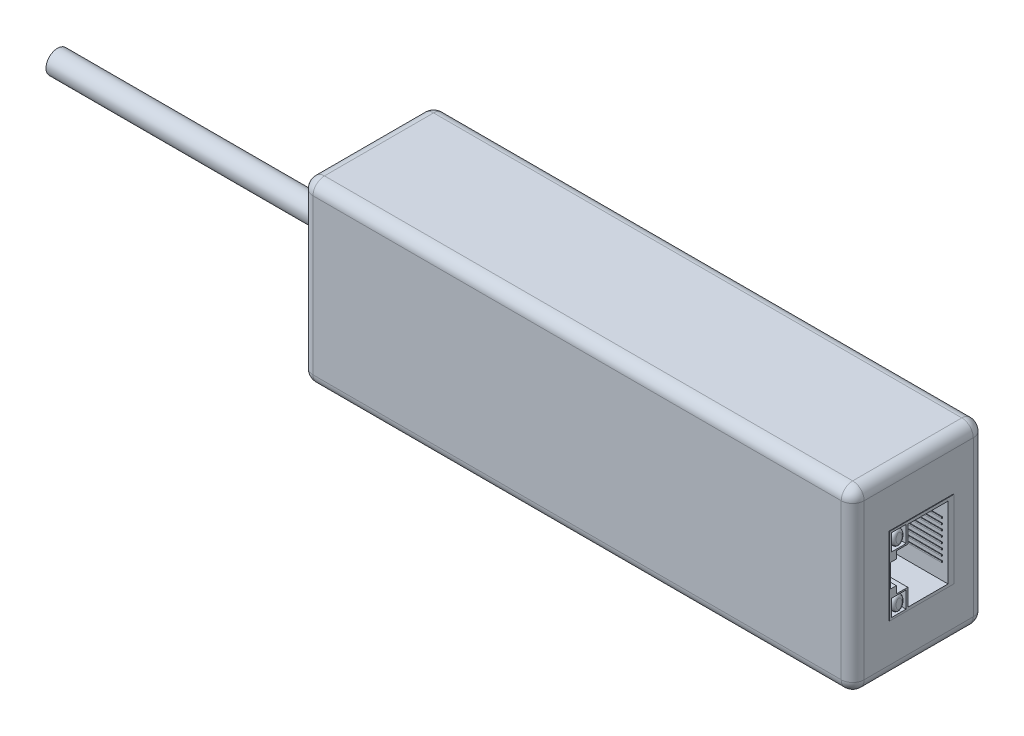
SolidWorks part; units mm, degrees
material "ABS"
ref_plane "前基準面" through (0, 0, 0) normal (0, 0, 1) x (1, 0, 0)
ref_plane "上基準面" through (0, 0, 0) normal (0, 1, 0) x (1, 0, 0)
ref_plane "右基準面" through (0, 0, 0) normal (1, 0, 0) x (0, 0, -1)
sketch "草圖1" plane through (0, 0, 0) normal (0, 0, 1) x (1, 0, 0)
  line L1 (-48, 15.5) -> (48, 15.5)
  line L2 (-48, 15.5) -> (-48, -15.5)
  line L3 (-48, -15.5) -> (48, -15.5)
  line L4 (48, 15.5) -> (48, -15.5)
  line L5 (-48, 15.5) -> (48, -15.5) construction
  line L6 (-48, -15.5) -> (48, 15.5) construction
  point P0 (0, 0)
  dimension "D1" = 96
  dimension "D2" = 31
extrude "填料-伸長1" add sketch "草圖1" along normal mid plane 23
sketch "草圖2" plane through (0, 0, -11.5) normal (0, 0, -1) x (-1, 0, 0)
  line L0 (20.25, 0) -> (3.25, 0) construction
  line L1 (23, -7) -> (17.5, -7)
  line L2 (23, -7) -> (23, 7)
  line L3 (23, 7) -> (17.5, 7)
  line L4 (17.5, -7) -> (17.5, 7)
  line L5 (23, -7) -> (17.5, 7) construction
  line L6 (23, 7) -> (17.5, -7) construction
  line L7 (6, -7) -> (0.5, -7)
  line L8 (6, -7) -> (6, 7)
  line L9 (6, 7) -> (0.5, 7)
  line L10 (0.5, -7) -> (0.5, 7)
  line L11 (6, -7) -> (0.5, 7) construction
  line L12 (6, 7) -> (0.5, -7) construction
  line L13 (-11, -7) -> (-16.5, -7)
  line L14 (-11, -7) -> (-11, 7)
  line L15 (-11, 7) -> (-16.5, 7)
  line L16 (-16.5, -7) -> (-16.5, 7)
  line L17 (-11, -7) -> (-16.5, 7) construction
  line L18 (-11, 7) -> (-16.5, -7) construction
  line L19 (3.25, 0) -> (-13.75, 0) construction
  line L20 (48, 15.5) -> (48, -15.5) construction
  point P0 (20.25, 0)
  point P5 (3.25, 0)
  point P10 (-13.75, 0)
  dimension "D1" = 5.5
  dimension "D2" = 14
  dimension "D3" = 11.5
  dimension "D4" = 25
extrude "除料-伸長1" cut sketch "草圖2" against normal blind 10
sketch "草圖3" plane through (48, 0, 0) normal (1, 0, 0) x (0, 0, -1)
  line L0 (5, 6.25) -> (5, -6.25)
  line L1 (5, -6.25) -> (-2, -6.25)
  line L2 (-2, -6.25) -> (-2, -3.25)
  line L3 (-2, -3.25) -> (-4, -3.25)
  line L4 (-4, -3.25) -> (-4, -2)
  line L5 (-4, -2) -> (-5, -2)
  line L6 (-5, -2) -> (-5, 2)
  line L7 (-5, 2) -> (-4, 2)
  line L8 (-4, 2) -> (-4, 3.25)
  line L9 (-4, 3.25) -> (-2, 3.25)
  line L10 (-2, 3.25) -> (-2, 6.25)
  line L11 (-2, 6.25) -> (5, 6.25)
  line L12 (5, 0) -> (-5, 0) construction
  line L13 (-11.5, -15.5) -> (11.5, -15.5) construction
  point P2 (5, 0)
  point P16 (0, 0)
  point P19 (0, -15.5)
  dimension "D1" = 12.5
  dimension "D2" = 4
  dimension "D3" = 7
  dimension "D4" = 3
  dimension "D6" = 1
  dimension "D7" = 10
extrude "除料-伸長2" cut sketch "草圖3" against normal blind 12
sketch "草圖4" plane through (-48, 0, 0) normal (-1, 0, 0) x (0, 0, 1)
  line L0 (11.5, 15.5) -> (-11.5, 15.5) construction
  line L1 (-11.5, 15.5) -> (-11.5, -15.5) construction
  circle A0 centre (0, 0) radius 3
  point P4 (0, 15.5)
  point P8 (-11.5, 0)
  dimension "D1" = 6
extrude "填料-伸長2" add sketch "草圖4" along normal blind 4
fillet "圓角1" radius 2 12 edges at (-48, -15.5, 0) (0, -15.5, 11.5) (48, -15.5, 0) (0, -15.5, -11.5) (48, 15.5, 0) (0, 15.5, 11.5) (-48, 15.5, 0) (0, 15.5, -11.5) (-48, 0, 11.5) (-48, 0, -11.5) (48, 0, 11.5) (48, 0, -11.5)
split "分割1" trim tools "前基準面" bodies to split 104 resulting bodies 105 106
sketch "草圖5" plane through (-52, 0, 0) normal (-1, 0, 0) x (0, 0, 1)
  line L0 (0, -3) -> (0, 3) construction
  circle A0 centre (0, 0) radius 2
  dimension "D1" = 4
extrude "填料-伸長3" add sketch "草圖5" along normal blind 50
sketch "草圖6" plane through (0, 0, -1.5) normal (0, 0, -1) x (-1, 0, 0)
  line L0 (17.5, 7) -> (17.5, -7) construction
  line L1 (20, 6.5) -> (18.5, 6.5)
  line L2 (20, 6.5) -> (20, -6.5)
  line L3 (20, -6.5) -> (18.5, -6.5)
  line L4 (18.5, 6.5) -> (18.5, -6.5)
  line L5 (17.5, -7) -> (23, -7) construction
  line L6 (23, 7) -> (17.5, 7) construction
  dimension "D1" = 1
  dimension "D2" = 0.5
  dimension "D3" = 0.5
  dimension "D4" = 1.5
extrude "填料-伸長4" add sketch "草圖6" along normal up to surface (10 mm away) up to face at (0, 0, -11.5)
sketch "草圖7" plane through (-20, 0, 0) normal (-1, 0, 0) x (0, 0, 1)
  line L0 (-11.5, 0) -> (-1.5, 0) construction
  line L1 (-3, 5.55) -> (-10.5, 5.55)
  line L2 (-3, 5.55) -> (-3, 3.75)
  line L3 (-3, 3.75) -> (-10.5, 3.75)
  line L4 (-10.5, 5.55) -> (-10.5, 3.75)
  line L5 (-4.5, 2.25) -> (-10.5, 2.25)
  line L6 (-4.5, 2.25) -> (-4.5, 0.75)
  line L7 (-4.5, 0.75) -> (-10.5, 0.75)
  line L8 (-10.5, 2.25) -> (-10.5, 0.75)
  line L9 (-4.5, -0.75) -> (-10.5, -0.75)
  line L10 (-4.5, -0.75) -> (-4.5, -2.25)
  line L11 (-4.5, -2.25) -> (-10.5, -2.25)
  line L12 (-10.5, -0.75) -> (-10.5, -2.25)
  line L13 (-3, -5.55) -> (-10.5, -5.55)
  line L14 (-3, -5.55) -> (-3, -3.75)
  line L15 (-3, -3.75) -> (-10.5, -3.75)
  line L16 (-10.5, -5.55) -> (-10.5, -3.75)
  line L17 (-11.5, 6.5) -> (-11.5, -6.5) construction
  line L18 (-1.5, -6.5) -> (-1.5, 6.5) construction
  dimension "D1" = 1
  dimension "D2" = 1.5
  dimension "D3" = 6
  dimension "D4" = 1.5
  dimension "D5" = 1.8
  dimension "D6" = 1
  dimension "D7" = 3.75
  dimension "D8" = 7.5
extrude "填料-伸長5" add sketch "草圖7" along normal blind 0.1 and the other way blind 0.5
pattern_linear "直線複製排列1" count 3 spacing 17 along (1, 0, 0) of "填料-伸長4", "填料-伸長5"
sketch "草圖8" plane through (48, 0, 0) normal (1, 0, 0) x (0, 0, -1)
  line L0 (5, 6.25) -> (-2, 6.25) construction
  line L1 (6, 6.75) -> (-5.2, 6.75)
  line L2 (6, 6.75) -> (6, -6.75)
  line L3 (6, -6.75) -> (-5.2, -6.75)
  line L4 (-5.2, 6.75) -> (-5.2, -6.75)
  line L5 (-2, -6.25) -> (5, -6.25) construction
  line L6 (-5, 2) -> (-5, -2) construction
  line L7 (5, -6.25) -> (5, 6.25) construction
  line L8 (5, 6.25) -> (-2, 6.25)
  line L9 (-2, 6.25) -> (-2, 3.25)
  line L10 (-2, 3.25) -> (-4, 3.25)
  line L11 (-4, 3.25) -> (-4, 2)
  line L12 (-4, 2) -> (-5, 2)
  line L13 (-5, 2) -> (-5, -2)
  line L14 (-5, -2) -> (-4, -2)
  line L15 (-4, -2) -> (-4, -3.25)
  line L16 (-4, -3.25) -> (-2, -3.25)
  line L17 (-2, -3.25) -> (-2, -6.25)
  line L18 (-2, -6.25) -> (5, -6.25)
  line L19 (5, -6.25) -> (5, 6.25)
  line M5 (5, 6.25) -> (5, -6.25)
  line M6 (5, -6.25) -> (-2, -6.25)
  line M7 (-2, -6.25) -> (-2, -3.25)
  line M8 (-2, -3.25) -> (-4, -3.25)
  line M9 (-4, -3.25) -> (-4, -2)
  line M10 (-4, -2) -> (-5, -2)
  line M11 (-5, -2) -> (-5, 2)
  line M12 (-5, 2) -> (-4, 2)
  line M13 (-4, 2) -> (-4, 3.25)
  line M14 (-4, 3.25) -> (-2, 3.25)
  line M15 (-2, 3.25) -> (-2, 6.25)
  line M16 (-2, 6.25) -> (5, 6.25)
  dimension "D1" = 0.5
  dimension "D2" = 0.5
  dimension "D3" = 0.2
  dimension "D4" = 1
extrude "填料-伸長6" add sketch "草圖8" along normal blind 0.1 and the other way blind 0.1 contours L1 L4 L3 L2 M16 M5 M6 M7 M8 M9 M10 M11 M12 M13 M14 M15
sketch "草圖9" plane through (48.1, 0, 0) normal (1, 0, 0) x (0, 0, -1)
  line L0 (-4, 3.25) -> (-2, 3.25) construction
  line L1 (-2.3, 3.4963) -> (-4.8, 3.4963)
  line L2 (-2.3, 3.4963) -> (-2.3, 6.3963)
  line L3 (-2.3, 6.3963) -> (-4.8, 6.3963)
  line L4 (-4.8, 3.4963) -> (-4.8, 6.3963)
  line L5 (-2.3, -3.4963) -> (-4.8, -3.4963)
  line L6 (-2.3, -3.4963) -> (-2.3, -6.3963)
  line L7 (-2.3, -6.3963) -> (-4.8, -6.3963)
  line L8 (-4.8, -3.4963) -> (-4.8, -6.3963)
  line L9 (-2, 3.25) -> (-2, 6.25) construction
  line L10 (5, 0) -> (-5, 0) construction
  line L11 (5, 6.25) -> (5, -6.25) construction
  line L12 (-5, -2) -> (-5, 2) construction
  dimension "D1" = 2.9
  dimension "D2" = 2.5
  dimension "D3" = 0.2463
  dimension "D4" = 0.3
extrude "除料-伸長3" cut sketch "草圖9" against normal blind 5 contours L2 L1 L4 L3 | L6 L5 L8 L7
sketch "草圖10" plane through (43.1, 0, 0) normal (1, 0, 0) x (0, 0, -1)
  line L0 (-3.55, 6.3963) -> (-3.55, 3.4963) construction
  line L4 (-2.3, 6.3963) -> (-4.8, 6.3963) construction
  line L5 (-2.3, 3.4963) -> (-4.8, 3.4963) construction
  ellipse E0 centre (-3.55, 4.9463) end of major axis (-3.55, 3.5963) minor radius 1
  dimension "D1" = 2
  dimension "D2" = 2.7
extrude "填料-伸長9" add sketch "草圖10" along normal blind 5
fillet "圓角2" radius 0.5 1 edges at (48.1, 6.2963, 3.55)
mirror "鏡射1" about plane through (0, 0, 0) normal (0, 1, 0) of "圓角2", "填料-伸長9"
sketch "草圖11" plane through (0, 0, -5) normal (0, 0, 1) x (1, 0, 0)
  line L0 (36, -6.25) -> (48.1, -6.25) construction
  line L1 (47.1, -3.25) -> (37.1, -3.25)
  line L2 (47.1, -3.25) -> (47.1, -3.5)
  line L3 (47.1, -3.5) -> (37.1, -3.5)
  line L4 (37.1, -3.25) -> (37.1, -3.5)
  line L5 (48.1, 6.25) -> (48.1, -6.25) construction
  dimension "D1" = 10
  dimension "D2" = 3
  dimension "D3" = 1
  dimension "D4" = 0.25
extrude "填料-伸長10" add sketch "草圖11" along normal blind 0.1
pattern_linear "直線複製排列2" count 8 spacing 0.95 along (0, 1, 0) of "填料-伸長10"
